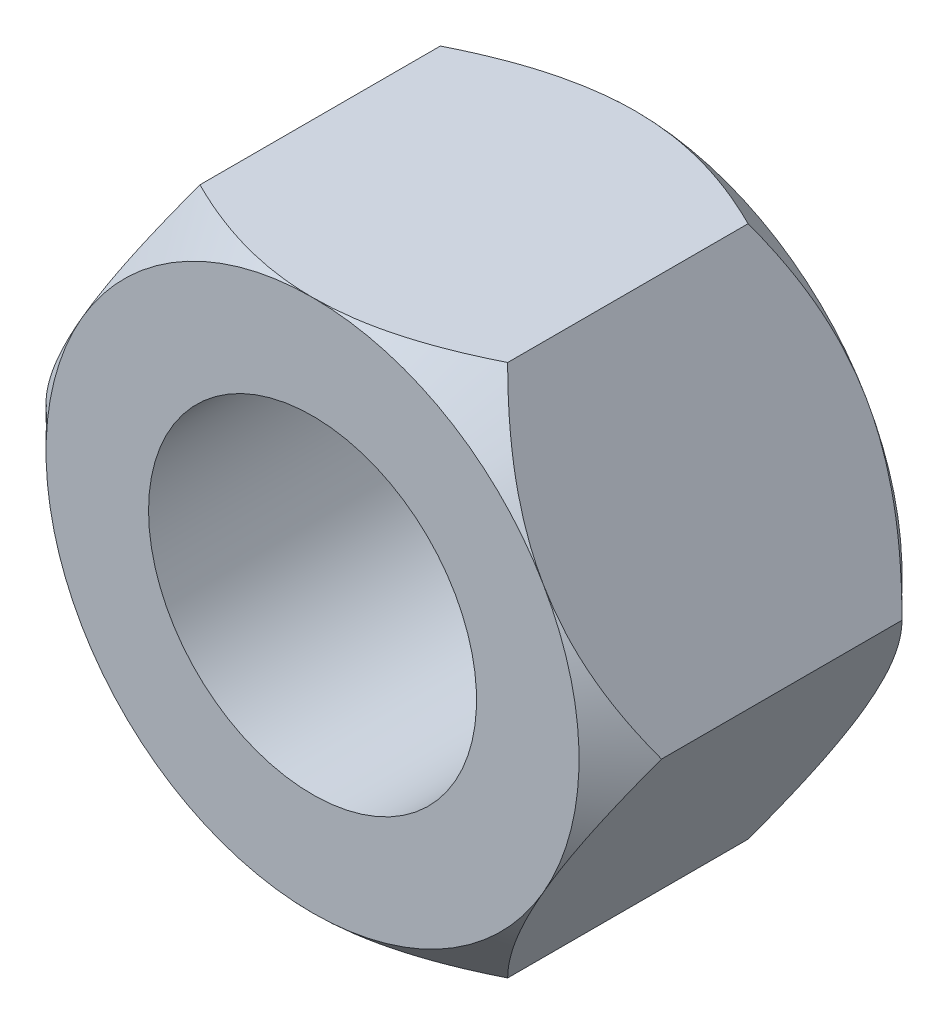
SolidWorks part; units mm, degrees
material "Plain Carbon Steel"
ref_plane "Front Plane" through (0, 0, 0) normal (0, 0, 1) x (1, 0, 0)
ref_plane "Top Plane" through (0, 0, 0) normal (0, 1, 0) x (1, 0, 0)
ref_plane "Right Plane" through (0, 0, 0) normal (1, 0, 0) x (0, 0, -1)
sketch "Sketch1" plane through (0, 0, 0) normal (0, 0, 1) x (1, 0, 0)
  line L0 (0, 0) -> (0, 22.4226) construction
  line L1 (-11.9151, 20.6375) -> (-23.8301, 0)
  line L2 (-23.8301, 0) -> (-11.9151, -20.6375)
  line L3 (-11.9151, -20.6375) -> (11.9151, -20.6375)
  line L4 (11.9151, -20.6375) -> (23.8301, 0)
  line L5 (23.8301, 0) -> (11.9151, 20.6375)
  line L6 (11.9151, 20.6375) -> (-11.9151, 20.6375)
  circle A0 centre (0, 0) radius 20.6375 construction
  circle A1 centre (0, 0) radius 12.7
  dimension "D2" = 25.4
  dimension "D1" = 41.275
extrude "Boss-Extrude1" add sketch "Sketch1" along normal blind 25.0031
sketch "Sketch2" plane through (0, 0, 0) normal (1, 0, 0) x (0, 0, -1)
  line L0 (-25.0031, 20.6375) -> (-18.6531, 26.9875)
  line L1 (-18.6531, 26.9875) -> (-31.3531, 26.9875)
  line L2 (-31.3531, 26.9875) -> (-31.3531, 14.2875)
  line L3 (-31.3531, 14.2875) -> (-25.0031, 20.6375)
  line L4 (-25.0031, 20.6375) -> (0, 20.6375) construction
  line L5 (-12.5016, 20.6375) -> (-12.5016, 41.3411) construction
  line L6 (6.35, 14.2875) -> (0, 20.6375)
  line L7 (6.35, 26.9875) -> (6.35, 14.2875)
  line L8 (-6.35, 26.9875) -> (6.35, 26.9875)
  line L9 (0, 20.6375) -> (-6.35, 26.9875)
  dimension "D1" = 45
  dimension "D2" = 12.7
sweep "Cut-Sweep1" cut profiles "Sketch2" path edge at (12.7, 0, 25.0031)
